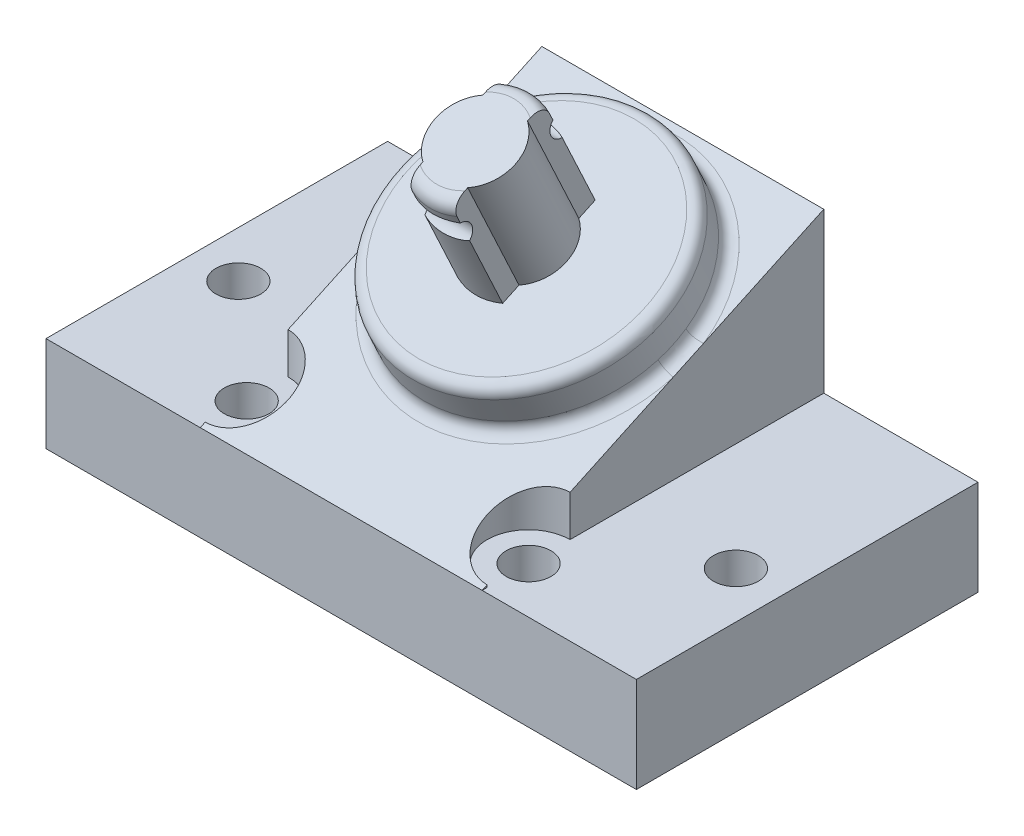
SolidWorks part; units mm, degrees
ref_plane "Front Plane" through (0, 0, 0) normal (0, 0, 1) x (1, 0, 0)
ref_plane "Top Plane" through (0, 0, 0) normal (0, 1, 0) x (1, 0, 0)
ref_plane "Right Plane" through (0, 0, 0) normal (1, 0, 0) x (0, 0, -1)
sketch "Sketch1" plane through (0, 0, 0) normal (0, 0, 1) x (1, 0, 0)
  line L0 (-17.8, 5.75) -> (17.8, 5.75)
  line L1 (17.8, 5.75) -> (17.8, 0)
  line L2 (17.8, 0) -> (12.2, 0)
  line L3 (12.2, 0) -> (12.2, 2.75)
  line L4 (12.2, 2.75) -> (-12.2, 2.75)
  line L5 (-12.2, 2.75) -> (-12.2, 0)
  line L6 (-12.2, 0) -> (-17.8, 0)
  line L7 (-17.8, 0) -> (-17.8, 5.75)
  line L8 (-12.2, 0) -> (12.2, 0) construction
  dimension "D1" = 35.6
  dimension "D2" = 24.4
  dimension "D3" = 3
  dimension "D4" = 2.75
extrude "Boss-Extrude1" add sketch "Sketch1" along normal mid plane 15
sketch "Sketch8" plane through (0, 0, 7.5) normal (0, 0, 1) x (1, 0, 0)
  line L1 (-17.8, 0) -> (17.8, 0)
  line L2 (-17.8, 0) -> (-17.8, 5.75)
  line L3 (-17.8, 5.75) -> (17.8, 5.75)
  line L4 (17.8, 0) -> (17.8, 5.75)
  line L5 (-17.8, 0) -> (17.8, 5.75) construction
  line L6 (-17.8, 5.75) -> (17.8, 0) construction
  point P0 (0, 2.875)
extrude "Boss-Extrude4" add sketch "Sketch8" along normal blind 5.6
sketch "Sketch11" plane through (0, 0, 0) normal (1, 0, 0) x (0, 0, -1)
  line L0 (-13.1, 5.75) -> (7.5, 15.3559)
  line L1 (7.5, 15.3559) -> (7.5, 5.75)
  line L2 (7.5, 5.75) -> (-13.1, 5.75)
  dimension "D1" = 25
extrude "Boss-Extrude5" add sketch "Sketch11" along normal mid plane 17
sketch "Sketch3" plane through (0, -0.8259, 27.2021) normal (0, -0.9063, -0.4226) x (1, 0, 0)
  line L0 (0, -15.5599) -> (0, -38.2895) construction
  line L4 (8.5, -15.5599) -> (-8.5, -15.5599) construction
  line L5 (8.5, -38.2895) -> (-8.5, -38.2895) construction
  circle A0 centre (0, -29.2895) radius 7.86
  dimension "D1" = 15.72
  dimension "D2" = 9
extrude "Boss-Extrude2" add sketch "Sketch3" against normal blind 3
fillet "Fillet4" radius 0.7 2 edges at (0, 17.5931, -5.199) (0, 14.8742, -6.4668)
sketch "Sketch5" plane through (0, 12.4595, 5.81) normal (0, 0.9063, 0.4226) x (1, 0, 0)
  line L0 (1.35, 6.2774) -> (1.35, 7.3639)
  line L2 (-1.35, 1.2101) -> (-1.35, 2.2967)
  line L4 (1.35, 1.2101) -> (1.35, 2.2967)
  line L7 (-1.35, 6.2774) -> (-1.35, 7.3639)
  arc A0 (-1.35, 6.2774) -> (-1.35, 2.2967) centre (0, 4.287) ccw
  arc A1 (1.35, 2.2967) -> (1.35, 6.2774) centre (0, 4.287) ccw
  arc A2 (-1.35, 1.2101) -> (1.35, 1.2101) centre (0, 4.287) ccw
  arc A3 (1.35, 7.3639) -> (-1.35, 7.3639) centre (0, 4.287) ccw
  circle A4 centre (0, 4.287) radius 7.16 construction
  dimension "D1" = 4.81
  dimension "D3" = 6.72
  dimension "D2" = 2.7
extrude "Boss-Extrude3" add sketch "Sketch5" along normal blind 7.32
sketch "Sketch6" plane through (1.35, 0, 0) normal (1, 0, 0) x (0, 0, -1)
  line L0 (-8.0634, 19.4855) -> (-4.9698, 12.8513) construction
  line L1 (1.1206, 15.6913) -> (-1.973, 22.3255) construction
  line L2 (4.5645, 17.2972) -> (-8.4138, 11.2454) construction
  line L3 (-7.2393, 17.7182) -> (-1.1489, 20.5582) construction
  line L4 (-3.2143, 21.7466) -> (-2.2296, 22.2058) construction
  circle A0 centre (-7.2393, 17.7182) radius 0.715
  circle A1 centre (-1.1489, 20.5582) radius 0.715
  point P8 (-6.5913, 18.0203)
  point P9 (-1.7969, 20.256)
  dimension "D1" = 5.29
  dimension "D2" = 5.37
extrude "Cut-Extrude2" cut sketch "Sketch6" against normal through all
fillet "Fillet5" radius 0.8 2 edges at (0, 22.3255, 1.973) (0, 19.4855, 8.0634)
sketch "Sketch9" plane through (0, 5.75, 0) normal (0, 1, 0) x (1, 0, 0)
  line L0 (17.8, -13.1) -> (8.5, -13.1) construction
  line L1 (-17.8, -13.1) -> (-17.8, 7.5) construction
  line L2 (15, -4.3) -> (-15, -4.3) construction
  line L3 (8.5, -10.3) -> (-8.5, -10.3) construction
  line L4 (0, 0) -> (0, -4.3) construction
  line L5 (0, -4.3) -> (0, -10.3) construction
  circle A0 centre (-8.5, -10.3) radius 1.35
  circle A1 centre (-15, -4.3) radius 1.35
  circle A2 centre (8.5, -10.3) radius 1.35
  circle A3 centre (15, -4.3) radius 1.35
  dimension "D1" = 2.7
  dimension "D2" = 2.8
  dimension "D3" = 2.8
  dimension "D4" = 17
  dimension "D5" = 6
extrude "Cut-Extrude3" cut sketch "Sketch9" against normal through all
sketch "Sketch12" plane through (0, 5.75, 0) normal (0, 1, 0) x (-1, 0, 0)
  circle A0 centre (8.5, 10.3) radius 2.5
  circle A2 centre (-8.5, 10.3) radius 2.5
  dimension "D1" = 5
extrude "Cut-Extrude4" cut sketch "Sketch12" along normal through all
